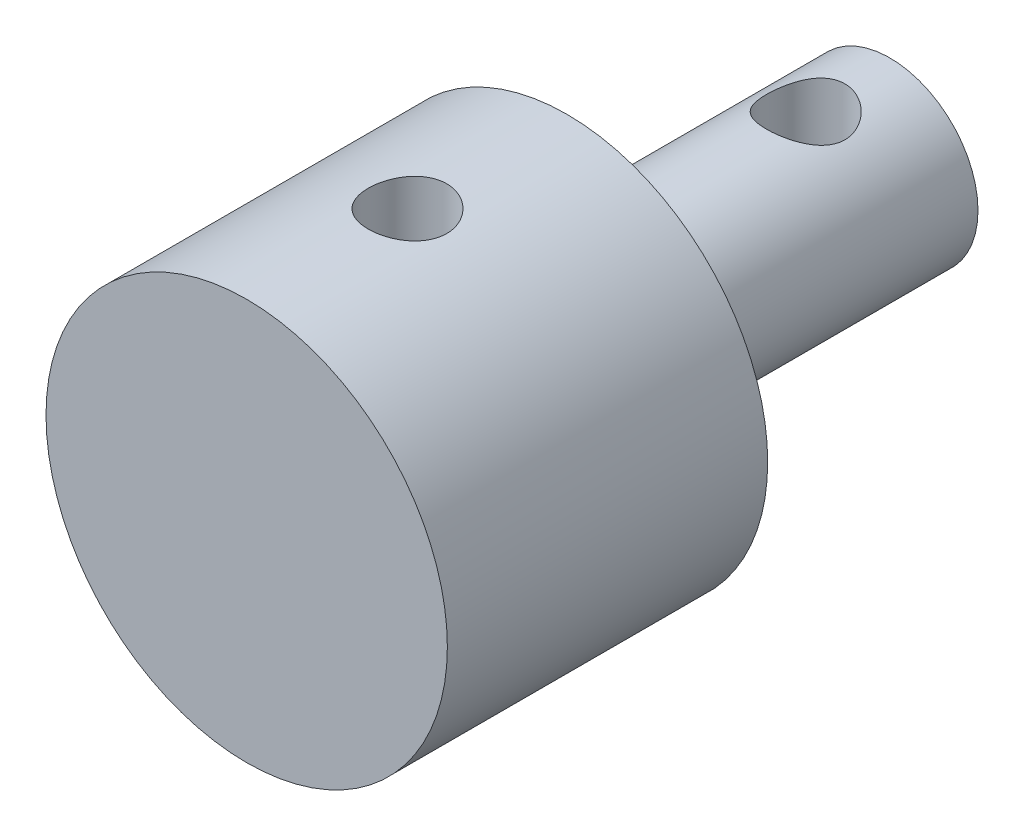
SolidWorks part; units mm, degrees
ref_plane "Front" through (0, 0, 0) normal (0, 0, 1) x (1, 0, 0)
ref_plane "Top" through (0, 0, 0) normal (0, 1, 0) x (1, 0, 0)
ref_plane "Right" through (0, 0, 0) normal (1, 0, 0) x (0, 0, -1)
sketch "Sketch1" plane through (0, 0, 0) normal (0, 0, 1) x (1, 0, 0)
  circle A0 centre (0, 0) radius 7.925
extrude "Extrude1" add sketch "Sketch1" along normal blind 25.4
sketch "Sketch2" plane through (0, 0, 0) normal (0, 0, 1) x (1, 0, 0)
  circle A0 centre (0, 0) radius 3.48
extrude "Cut-Extrude1" cut sketch "Sketch2" along normal blind 12.75 flip side to cut
sketch "Sketch3" plane through (0, 0, 0) normal (0, 1, 0) x (1, 0, 0)
  line L0 (0, -25.4) -> (0, -12.75) construction
  circle A0 centre (0, -3.325) radius 1.55
extrude "Cut-Extrude2" cut sketch "Sketch3" against normal through all and the other way through all
sketch "Sketch4" plane through (0, 0, 0) normal (0, 1, 0) x (1, 0, 0)
  line L0 (0, -25.4) -> (0, -12.75) construction
  circle A0 centre (0, -19.05) radius 1.55
  circle A1 centre (0, -3.325) radius 1.55 construction
  dimension "D1" = 3.1
  dimension "D2" = 15.725
extrude "Cut-Extrude3" cut sketch "Sketch4" against normal through all and the other way through all
